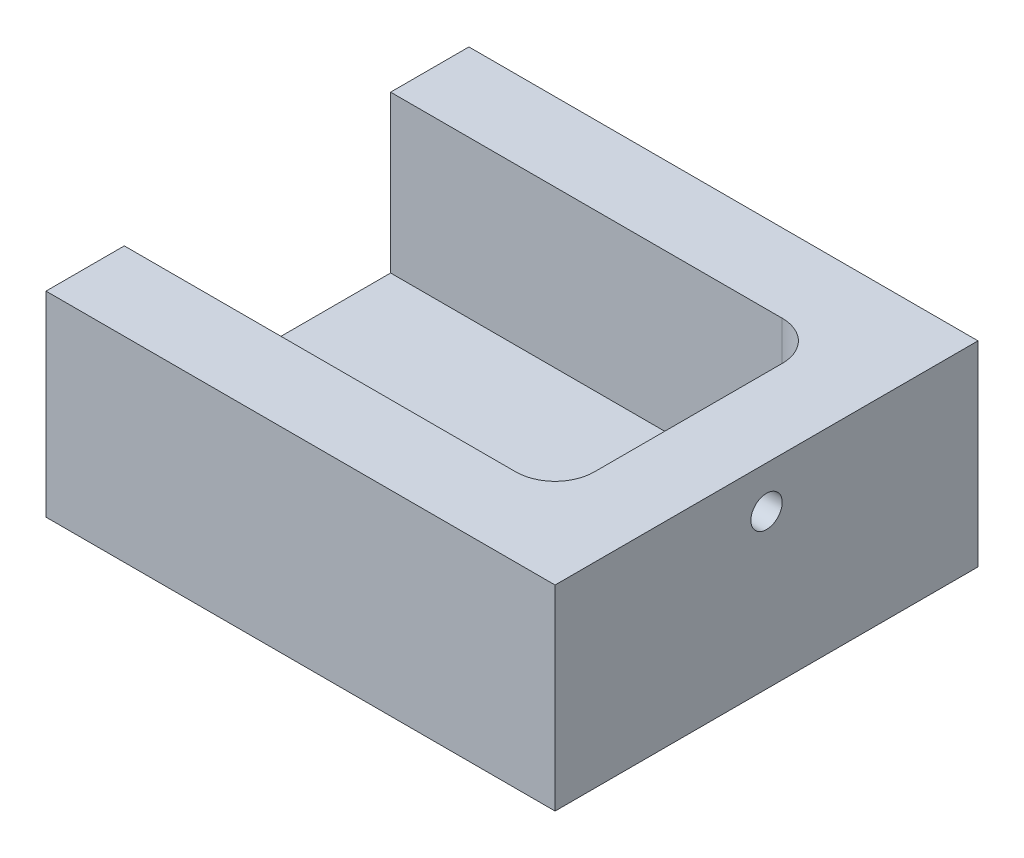
SolidWorks part; units mm, degrees
material "PVC Rigid"
ref_plane "Front Plane" through (0, 0, 0) normal (0, 0, 1) x (1, 0, 0)
ref_plane "Top Plane" through (0, 0, 0) normal (0, 1, 0) x (1, 0, 0)
ref_plane "Right Plane" through (0, 0, 0) normal (1, 0, 0) x (0, 0, -1)
sketch "Sketch1" plane through (0, 0, 0) normal (0, 1, 0) x (1, 0, 0)
  line L1 (0, 0) -> (65, 0)
  line L2 (0, 0) -> (0, 54)
  line L3 (0, 54) -> (65, 54)
  line L4 (65, 0) -> (65, 54)
  dimension "D1" = 54
  dimension "D2" = 65
extrude "Boss-Extrude1" add sketch "Sketch1" along normal blind 25
sketch "Sketch2" plane through (0, 25, 0) normal (0, 1, 0) x (1, 0, 0)
  line L0 (0, 54) -> (0, 0) construction
  line L1 (0, 44) -> (55, 44)
  line L2 (0, 44) -> (0, 10)
  line L3 (0, 10) -> (55, 10)
  line L4 (55, 44) -> (55, 10)
  line L5 (65, 0) -> (65, 54) construction
  line L6 (65, 54) -> (0, 54) construction
  line L7 (0, 0) -> (65, 0) construction
  dimension "D1" = 10
  dimension "D2" = 10
  dimension "D3" = 10
extrude "Cut-Extrude1" cut sketch "Sketch2" against normal blind 20
sketch "Sketch3" plane through (65, 0, 0) normal (1, 0, 0) x (0, 0, -1)
  line L0 (0, 25) -> (54, 25) construction
  circle A0 centre (27, 19.64) radius 2
  point P2 (0, 0)
  point P5 (27, 25)
  point P9 (0, 0)
  dimension "D1" = 4
  dimension "D2" = 5.36
extrude "Cut-Extrude2" cut sketch "Sketch3" against normal through all
fillet "Fillet1" radius 5 2 edges at (55, 15, -10) (55, 15, -44)
